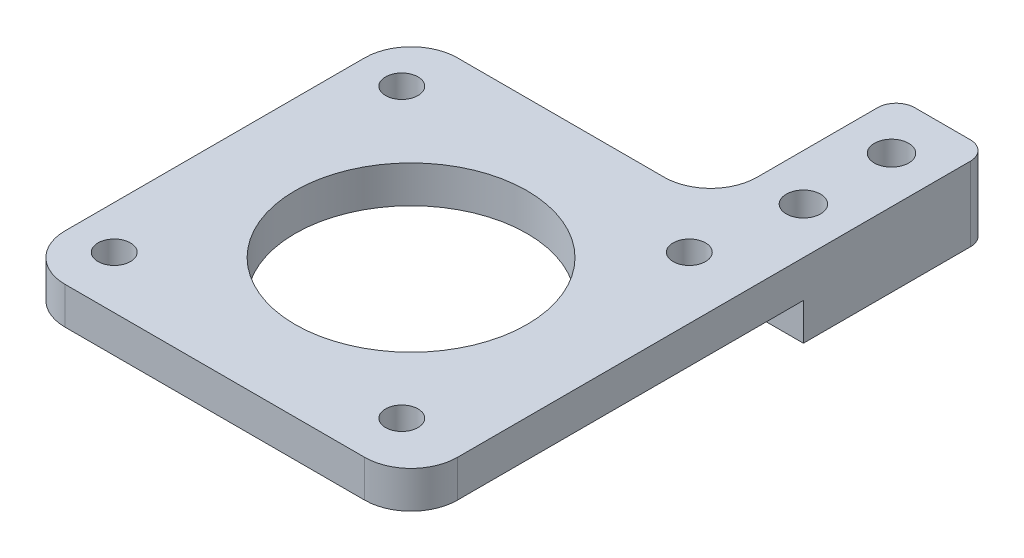
SolidWorks part; units mm, degrees
ref_plane "Front Plane" through (0, 0, 0) normal (0, 0, 1) x (1, 0, 0)
ref_plane "Top Plane" through (0, 0, 0) normal (0, 1, 0) x (1, 0, 0)
ref_plane "Right Plane" through (0, 0, 0) normal (1, 0, 0) x (0, 0, -1)
sketch "Sketch2" plane through (0, 0, 0) normal (0, 1, 0) x (1, 0, 0)
  line L9 (-30.65, 0) -> (-30.65, 42.3)
  line L12 (-30.65, 0) -> (11.65, 0)
  line L13 (11.65, 42.3) -> (11.65, 0)
  line L14 (-30.65, 42.3) -> (1.65, 42.3)
  line L15 (1.65, 42.3) -> (1.65, 62.3)
  line L16 (1.65, 62.3) -> (11.65, 62.3)
  line L17 (11.65, 62.3) -> (11.65, 42.3)
  circle A0 centre (5, 5.65) radius 1.75
  circle A1 centre (5, 36.65) radius 1.75
  circle A4 centre (-26, 5.65) radius 1.75
  circle A5 centre (-26, 36.65) radius 1.75
  circle A6 centre (-9.5, 21.15) radius 12.5
  circle A7 centre (6.65, 56.8) radius 1.85
  circle A8 centre (6.65, 47.3) radius 1.85
  point P13 (1.65, 52.3)
  dimension "D2" = 3.5
  dimension "D3" = 3.5
  dimension "D10" = 3.7
  dimension "D11" = 3.7
  dimension "D19" = 3.5
  dimension "D21" = 3.5
  dimension "D7" = 25
  dimension "D4" = 20
  dimension "D5" = 10
  dimension "D6" = 42.3
  dimension "D8" = 31
  dimension "D9" = 21.15
  dimension "D12" = 0
  dimension "D13" = 9.5
  dimension "D14" = 5
  dimension "D15" = 5
  dimension "D20" = 31
  dimension "D22" = 31
  dimension "D23" = 31
extrude "Boss-Extrude1" add sketch "Sketch2" along normal blind 4
fillet "Fillet1" radius 5 3 edges at (11.65, 2, 0) (-30.65, 2, 0) (-30.65, 2, -42.3)
fillet "Fillet8" radius 5 1 edges at (1.65, 2, -42.3)
sketch "Sketch5" plane through (0, 0, 0) normal (0, -1, 0) x (1, 0, 0)
  line L1 (11.65, -62.3) -> (1.65, -62.3)
  line L2 (11.65, -62.3) -> (11.65, -42.3)
  line L5 (-3.35, -42.3) -> (11.65, -42.3)
  line L6 (1.65, -47.3) -> (1.65, -62.3)
  circle A0 centre (6.65, -47.3) radius 1.85
  circle A1 centre (6.65, -56.8) radius 1.85
  arc A2 (-3.35, -42.3) -> (1.65, -47.3) centre (-3.35, -47.3) cw
  arc A3 (1.65, -47.3) -> (-3.35, -42.3) centre (-3.35, -47.3) ccw construction
extrude "Boss-Extrude2" add sketch "Sketch5" along normal blind 4 contours L2 L5 A2 L6 L1 | A0 | A1
fillet "Fillet10" radius 2 2 edges at (11.65, 0, -62.3) (1.65, 0, -62.3)
